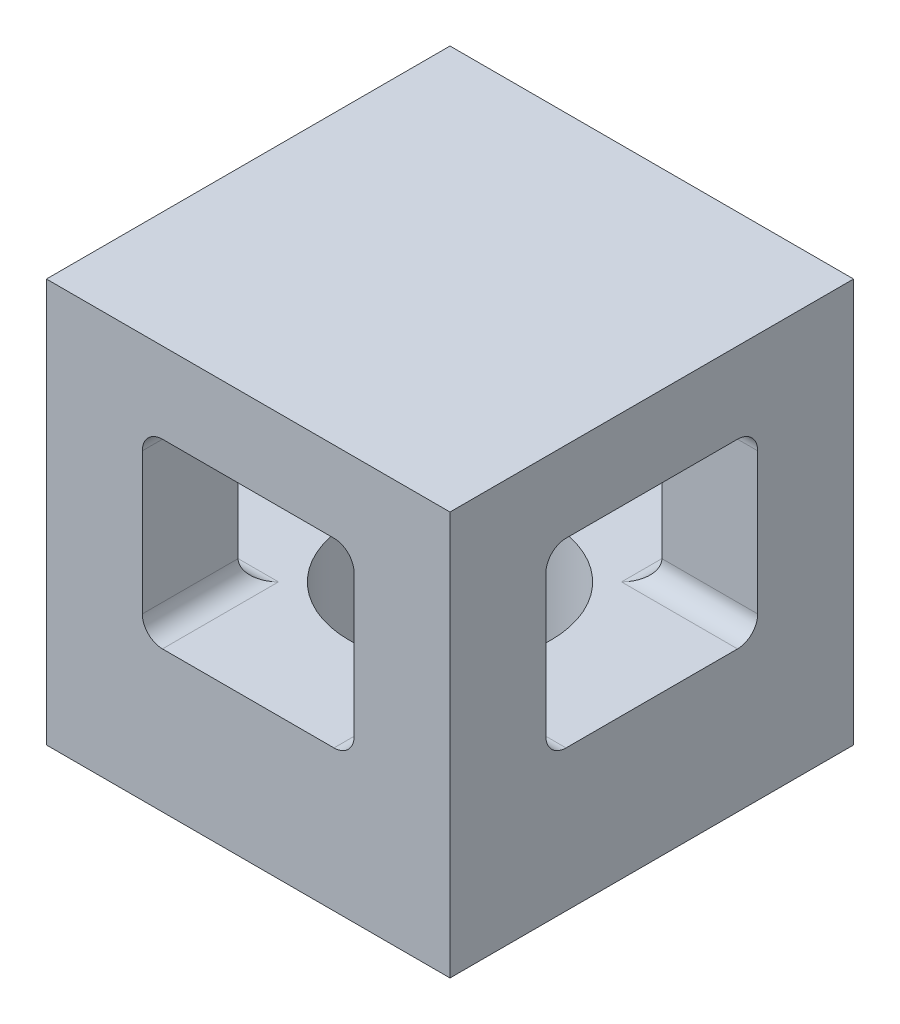
SolidWorks part; units mm, degrees
ref_plane "Front Plane" through (0, 0, 0) normal (0, 0, 1) x (1, 0, 0)
ref_plane "Top Plane" through (0, 0, 0) normal (0, 1, 0) x (1, 0, 0)
ref_plane "Right Plane" through (0, 0, 0) normal (1, 0, 0) x (0, 0, -1)
sketch "Sketch2" plane through (0, 0, 0) normal (0, 1, 0) x (1, 0, 0)
  line L1 (0, 0) -> (10.16, 0)
  line L2 (0, 0) -> (0, 10.16)
  line L3 (0, 10.16) -> (10.16, 10.16)
  line L4 (10.16, 0) -> (10.16, 10.16)
extrude "Boss-Extrude1" add sketch "Sketch2" along normal blind 10.16
sketch "Sketch3" plane through (0, 0, 0) normal (0, -1, 0) x (-1, 0, 0)
  circle A0 centre (-5.08, 5.08) radius 2.54
extrude "Cut-Extrude1" cut sketch "Sketch3" against normal blind 8.128
sketch "Sketch4" plane through (0, 0, 0) normal (0, 0, 1) x (1, 0, 0)
  line L1 (2.921, 8.128) -> (7.239, 8.128)
  line L2 (2.413, 7.62) -> (2.413, 4.064)
  line L3 (2.921, 3.556) -> (7.239, 3.556)
  line L4 (7.747, 7.62) -> (7.747, 4.064)
  arc A0 (2.413, 4.064) -> (2.921, 3.556) centre (2.921, 4.064) ccw
  arc A1 (2.921, 8.128) -> (2.413, 7.62) centre (2.921, 7.62) ccw
  arc A2 (7.239, 8.128) -> (7.747, 7.62) centre (7.239, 7.62) cw
  arc A3 (7.239, 3.556) -> (7.747, 4.064) centre (7.239, 4.064) ccw
  point P12 (0, 0)
  dimension "D1" = 0.508
  dimension "D2" = 0.508
  dimension "D3" = 0.508
  dimension "D4" = 0.508
sketch "Sketch6" plane through (10.16, 0, 0) normal (1, 0, 0) x (0, 0, -1)
  line L0 (2.921, 8.128) -> (7.239, 8.128)
  line L1 (2.413, 7.62) -> (2.413, 4.064)
  line L2 (2.921, 3.556) -> (7.239, 3.556)
  line L3 (7.747, 7.62) -> (7.747, 4.064)
  arc A0 (2.413, 4.064) -> (2.921, 3.556) centre (2.921, 4.064) ccw
  arc A1 (2.921, 8.128) -> (2.413, 7.62) centre (2.921, 7.62) ccw
  arc A2 (7.239, 8.128) -> (7.747, 7.62) centre (7.239, 7.62) cw
  arc A3 (7.239, 3.556) -> (7.747, 4.064) centre (7.239, 4.064) ccw
  dimension "D1" = 0.508
  dimension "D2" = 0.508
  dimension "D3" = 0.508
  dimension "D4" = 0.508
extrude "Cut-Extrude2" cut sketch "Sketch6" against normal blind 10.16
extrude "Cut-Extrude3" cut sketch "Sketch4" against normal blind 10.16
